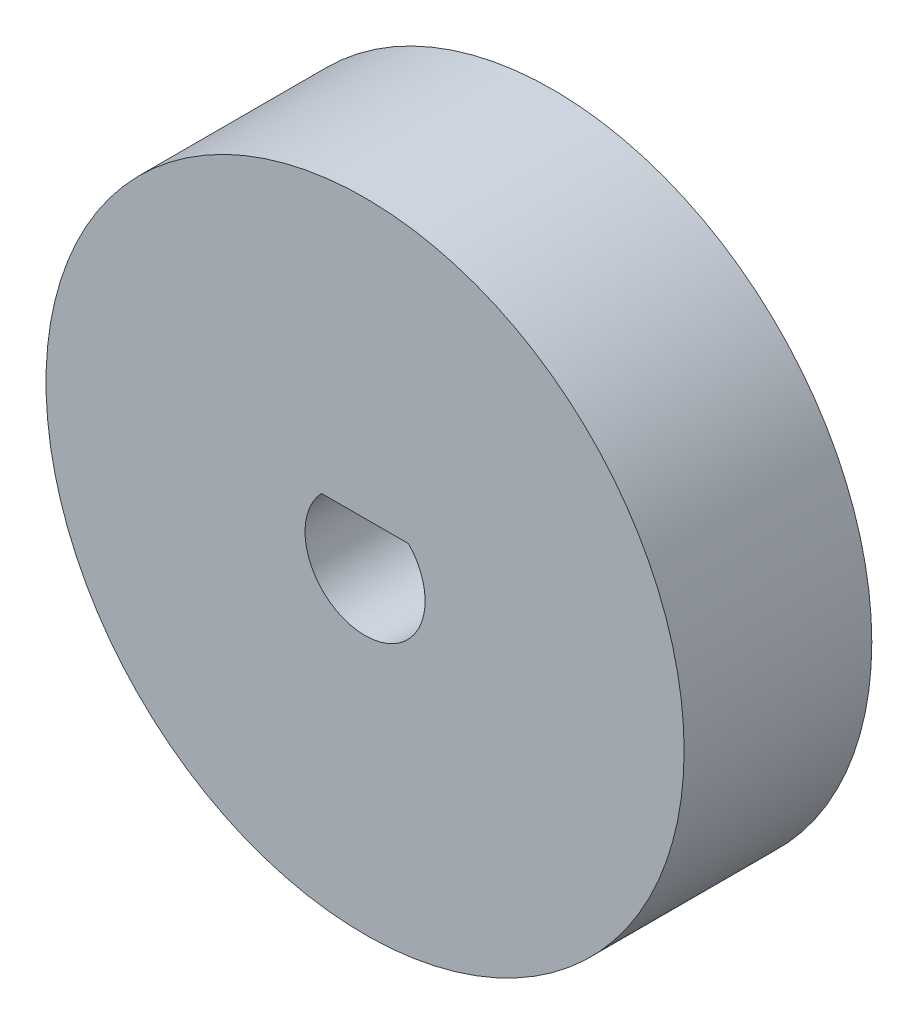
SolidWorks part; units mm, degrees
ref_plane "Front Plane" through (0, 0, 0) normal (0, 0, 1) x (1, 0, 0)
ref_plane "Top Plane" through (0, 0, 0) normal (0, 1, 0) x (1, 0, 0)
ref_plane "Right Plane" through (0, 0, 0) normal (1, 0, 0) x (0, 0, -1)
sketch "Sketch2" plane through (0, 0, 8) normal (0, 0, 1) x (1, 0, 0)
  line L1 (12.882, 1) -> (15.118, 1)
  line L2 (12.8381, 1.1) -> (15.1619, 1.1)
  circle A0 centre (14, 0) radius 8.5
  arc A1 (12.882, 1) -> (15.118, 1) centre (14, 0) ccw
  arc A2 (12.8381, 1.1) -> (15.1619, 1.1) centre (14, 0) ccw
  dimension "D1" = 17
  dimension "D2" = 0.1
extrude "Boss-Extrude1" add sketch "Sketch2" against normal blind 5 contours A0 A2 L2
